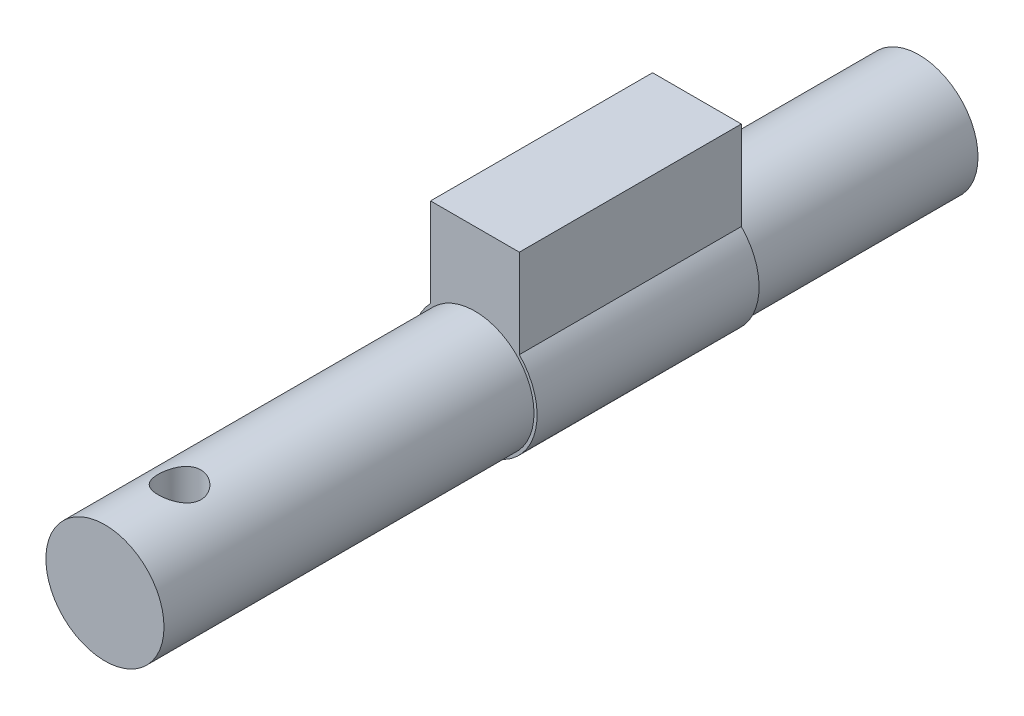
SolidWorks part; units mm, degrees
ref_plane "Front Plane" through (0, 0, 0) normal (0, 0, 1) x (1, 0, 0)
ref_plane "Top Plane" through (0, 0, 0) normal (0, 1, 0) x (1, 0, 0)
ref_plane "Right Plane" through (0, 0, 0) normal (1, 0, 0) x (0, 0, -1)
sketch "Sketch1" plane through (0, 0, 0) normal (0, 0, 1) x (1, 0, 0)
  circle A0 centre (-14.3839, -0.8549) radius 3.99
  dimension "D1" = 7.98
extrude "Boss-Extrude1" add sketch "Sketch1" along normal blind 15
sketch "Sketch6" plane through (0, 0, 15) normal (0, 0, 1) x (1, 0, 0)
  line L2 (-17.3839, 2.0845) -> (-17.3839, 8.0845)
  line L3 (-17.3839, 8.0845) -> (-11.3839, 8.0845)
  line L4 (-11.3839, 2.0845) -> (-11.3839, 8.0845)
  arc A0 (-17.3839, 2.0845) -> (-11.3839, 2.0845) centre (-14.3839, -0.8549) ccw
  circle A1 centre (-14.3839, -0.8549) radius 3.99 construction
  dimension "D1" = 0
  dimension "D5" = 6
  dimension "D6" = 6
extrude "Boss-Extrude7" add sketch "Sketch6" along normal blind 15
sketch "Sketch7" plane through (0, 0, 30) normal (0, 0, 1) x (1, 0, 0)
  circle A0 centre (-14.3839, -0.8549) radius 3.99
  arc A1 (-17.3839, 2.0845) -> (-11.3839, 2.0845) centre (-14.3839, -0.8549) ccw construction
  dimension "D1" = 0
  dimension "D2" = 7.98
extrude "Boss-Extrude8" add sketch "Sketch7" along normal blind 25
sketch "Sketch8" plane through (0, 8.0845, 0) normal (0, 1, 0) x (1, 0, 0)
  line L0 (-10.3939, -55) -> (-10.3939, -30) construction
  line L1 (-18.3739, -55) -> (-10.3939, -55) construction
  circle A0 centre (-14.3439, -50) radius 1.45
  dimension "D2" = 2.9
  dimension "D1" = 3.95
  dimension "D3" = 5
extrude "Cut-Extrude1" cut sketch "Sketch8" against normal blind 8
